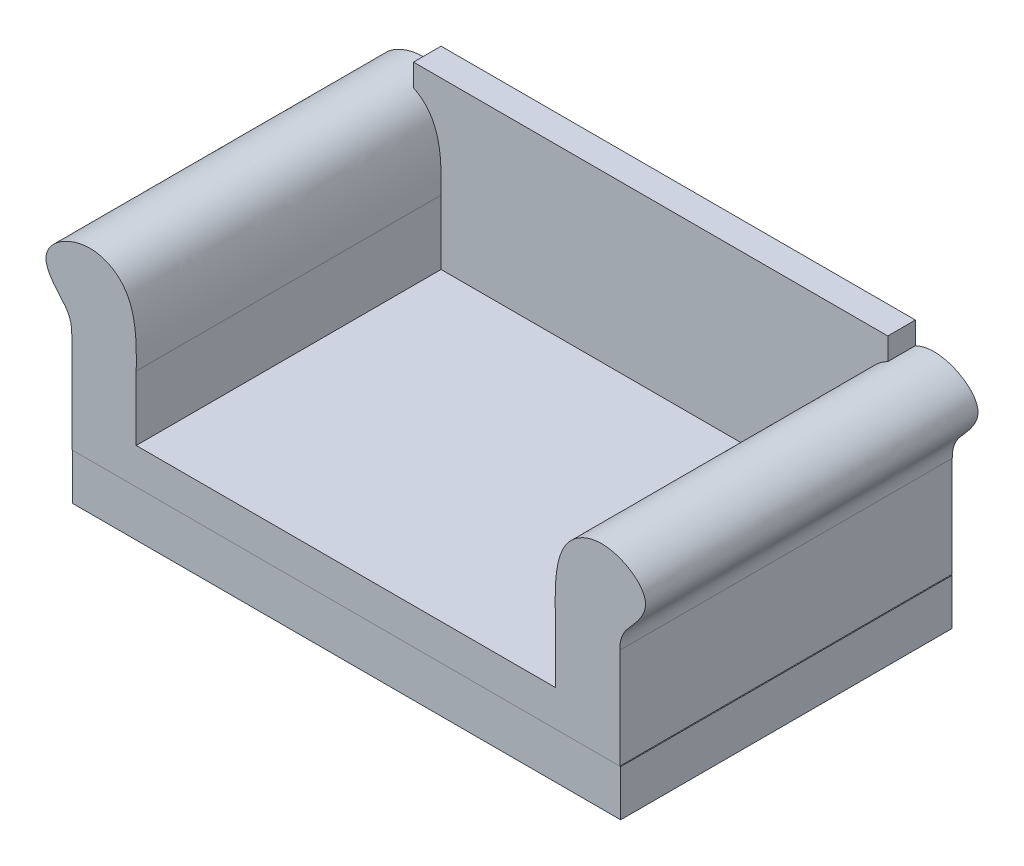
SolidWorks part; units mm, degrees
ref_plane "Front Plane" through (0, 0, 0) normal (0, 0, 1) x (1, 0, 0)
ref_plane "Top Plane" through (0, 0, 0) normal (0, 1, 0) x (1, 0, 0)
ref_plane "Right Plane" through (0, 0, 0) normal (1, 0, 0) x (0, 0, -1)
sketch "Sketch1" plane through (0, 0, 0) normal (0, 1, 0) x (1, 0, 0)
  line L1 (-755.65, -457.2) -> (755.65, -457.2) construction
  line L2 (-755.65, -457.2) -> (-755.65, 457.2) construction
  line L3 (-755.65, 457.2) -> (755.65, 457.2) construction
  line L4 (755.65, -457.2) -> (755.65, 457.2) construction
  line L5 (-755.65, -457.2) -> (755.65, 457.2) construction
  line L6 (-755.65, 457.2) -> (755.65, -457.2) construction
  line L7 (-755.65, 457.2) -> (-666.75, 457.2)
  line L8 (-755.65, 457.2) -> (-755.65, -457.2)
  line L9 (-755.65, -457.2) -> (-666.75, -457.2)
  line L10 (-666.75, 457.2) -> (-666.75, -457.2)
  line L11 (-711.2, -457.2) -> (-711.2, 457.2) construction
  line L12 (-755.65, 0) -> (-666.75, 0) construction
  line L13 (666.75, 457.2) -> (755.65, 457.2)
  line L14 (666.75, 457.2) -> (666.75, -457.2)
  line L15 (666.75, -457.2) -> (755.65, -457.2)
  line L16 (755.65, 457.2) -> (755.65, -457.2)
  line L17 (711.2, -457.2) -> (711.2, 457.2) construction
  line L18 (666.75, 0) -> (755.65, 0) construction
  line L19 (-666.75, 431.8) -> (666.75, 431.8)
  line L20 (-666.75, 431.8) -> (-666.75, 457.2)
  line L21 (-666.75, 457.2) -> (666.75, 457.2)
  line L22 (666.75, 431.8) -> (666.75, 457.2)
  line L23 (0, 457.2) -> (0, 431.8) construction
  line L24 (-666.75, 444.5) -> (666.75, 444.5) construction
  line L25 (-666.75, -457.2) -> (666.75, -457.2)
  line L26 (-666.75, -457.2) -> (-666.75, -431.8)
  line L27 (-666.75, -431.8) -> (666.75, -431.8)
  line L28 (666.75, -457.2) -> (666.75, -431.8)
  line L29 (0, -431.8) -> (0, -457.2) construction
  line L30 (-666.75, -444.5) -> (666.75, -444.5) construction
  line L31 (31.75, 431.8) -> (57.15, 431.8)
  line L32 (31.75, 431.8) -> (31.75, -431.8)
  line L33 (31.75, -431.8) -> (57.15, -431.8)
  line L34 (57.15, 431.8) -> (57.15, -431.8)
  line L35 (44.45, -431.8) -> (44.45, 431.8) construction
  line L36 (31.75, 0) -> (57.15, 0) construction
  point P0 (0, 0)
  point P140 (711.2, 0)
  point P190 (44.45, 0)
  point P309 (0, -444.5)
  point P335 (0, 444.5)
  point P376 (-711.2, 0)
  dimension "D1" = 914.4
  dimension "D3" = 88.9
  dimension "D4" = 25.4
  dimension "D5" = 25.4
  dimension "D6" = 25.4
  dimension "D7" = 787.4
  dimension "D2" = 698.5
extrude "Boss-Extrude1" add sketch "Sketch1" along normal blind 127 contours L10 L7 L8 L9 | L27 L10 L25 L14 | L16 L13 L14 L15 | L21 L10 L19 L14 | L34 L19 L32 L27
ref_plane "Plane1" through (0, 129.54, 0) normal (0, 1, 0) x (1, 0, 0)
sketch "Sketch2" plane through (0, 129.54, 0) normal (0, 1, 0) x (1, 0, 0)
  line L0 (755.65, 457.2) -> (755.65, -457.2) construction
  line L1 (-755.65, -457.2) -> (755.65, -457.2) construction
  line L2 (-755.65, 457.2) -> (-755.65, -457.2) construction
  line L3 (-755.65, 457.2) -> (755.65, 457.2) construction
  line L4 (755.65, 457.2) -> (755.65, -457.2)
  line L5 (-755.65, -457.2) -> (755.65, -457.2)
  line L6 (-755.65, 457.2) -> (-755.65, -457.2)
  line L7 (-755.65, 457.2) -> (755.65, 457.2)
ref_plane "Plane2" through (0, 0, 459.74) normal (0, 0, 1) x (1, 0, 0)
sketch "Sketch4" plane through (0, 0, 459.74) normal (0, 0, 1) x (1, 0, 0)
  line L0 (-755.65, 129.54) -> (755.65, 129.54) construction
  line L4 (-755.65, 0) -> (755.65, 0) construction
  line L5 (755.65, 0) -> (755.65, 127) construction
  line L6 (755.65, 127) -> (-755.65, 127) construction
  line L7 (-755.65, 127) -> (-755.65, 0) construction
  line L8 (-755.65, 129.54) -> (755.65, 129.54)
  line L12 (-755.65, 0) -> (755.65, 0)
  line L13 (755.65, 0) -> (755.65, 127)
  line L14 (755.65, 127) -> (-755.65, 127)
  line L15 (-755.65, 127) -> (-755.65, 0)
  line L16 (-755.65, 129.54) -> (-755.65, 406.4)
  line L17 (-577.85, 406.4) -> (-577.85, 228.6)
  line L18 (-577.85, 228.6) -> (577.85, 228.6)
  line L19 (0, 0) -> (0, 50000) construction
  line L20 (577.85, 406.4) -> (577.85, 228.6)
  line L21 (755.65, 129.54) -> (755.65, 406.4)
  spline S0 degree 3 poles (-755.65, 406.4) (-755.65, 451.0873) (-791.2169, 477.4334) (-855.3989, 573.8525) (-720.3037, 663.2325) (-568.8677, 589.8389) (-577.85, 447.6507) (-577.85, 406.4) knots 0 0 0 0 0.157243 0.266643 0.492649 0.701572 1 1 1 1
  spline S1 degree 3 poles (755.65, 406.4) (755.65, 451.0873) (791.2169, 477.4334) (855.3989, 573.8525) (720.3037, 663.2325) (568.8677, 589.8389) (577.85, 447.6507) (577.85, 406.4) knots 0 0 0 0 0.157243 0.266643 0.492649 0.701572 1 1 1 1
  point P47 (0, 228.6)
  dimension "D1" = 635
  dimension "D2" = 406.4
  dimension "D3" = 228.6
  dimension "D4" = 177.8
extrude "Boss-Extrude3" add sketch "Sketch4" against normal up to surface (916.94 mm away) separate body contours S0 L17 L18 L20 S1 L21 L8 L16 up to face at (0, 63.5, -457.2)
sketch "Sketch5" plane through (0, 228.6, 0) normal (0, 1, 0) x (1, 0, 0)
  line L0 (-755.65, 457.2) -> (755.65, 457.2) construction
  line L1 (-654.05, 457.2) -> (654.05, 457.2)
  line L2 (-654.05, 457.2) -> (-654.05, 381)
  line L3 (-654.05, 381) -> (654.05, 381)
  line L4 (577.85, 457.2) -> (-577.85, 457.2)
  line L5 (-577.85, 457.2) -> (-577.85, -459.74)
  line L6 (-577.85, -459.74) -> (577.85, -459.74)
  line L7 (577.85, -459.74) -> (577.85, 457.2)
  line L8 (577.85, 457.2) -> (-577.85, 457.2)
  line L9 (-577.85, 457.2) -> (-577.85, -459.74)
  line L10 (-577.85, -459.74) -> (577.85, -459.74)
  line L11 (577.85, -459.74) -> (577.85, 457.2)
  line L12 (654.05, 457.2) -> (654.05, 381)
  line L13 (0, 381) -> (0, 457.2) construction
  line L14 (-654.05, 419.1) -> (654.05, 419.1) construction
  point P112 (0, 419.1)
  dimension "D2" = 76.2
  dimension "D3" = 76.2
  dimension "D1" = 0
extrude "Boss-Extrude4" add sketch "Sketch5" along normal blind 457.2 contours L1 L12 L3 L2
equation "\"D5@Sketch1\"=\"D4@Sketch1\""
